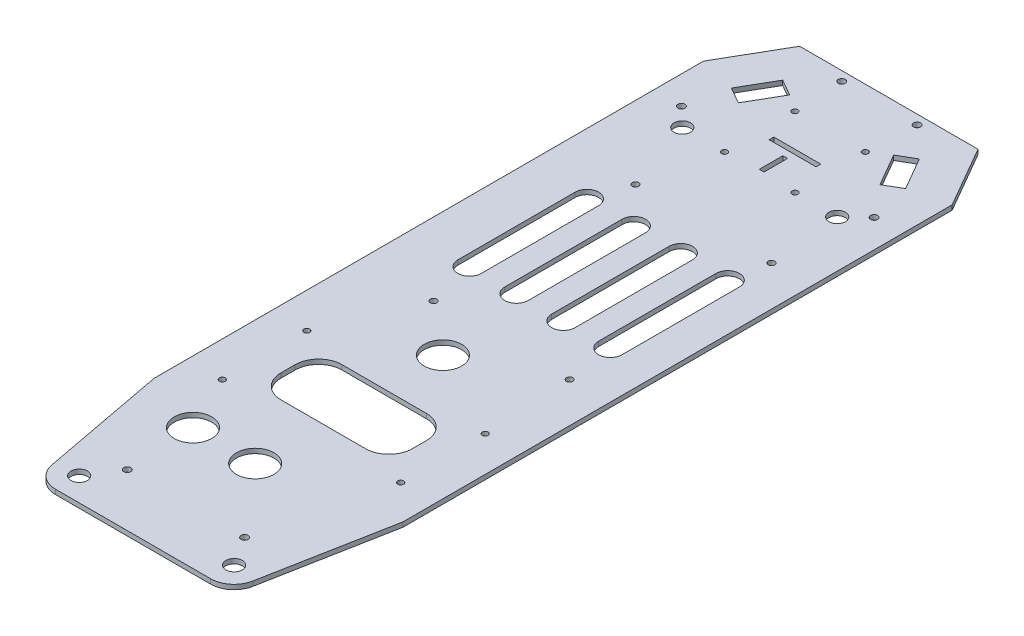
SolidWorks part; units mm, degrees
material "Epoxy, renforcé"
ref_plane "Plan de face" through (0, 0, 0) normal (0, 0, 1) x (1, 0, 0)
ref_plane "Plan de dessus" through (0, 0, 0) normal (0, 1, 0) x (1, 0, 0)
ref_plane "Plan de droite" through (0, 0, 0) normal (1, 0, 0) x (0, 0, -1)
sketch "Esquisse1" plane through (0, 0, 0) normal (0, 1, 0) x (1, 0, 0)
  line L0 (-33, 128.5) -> (33, 128.5) construction
  line L1 (33, 128.5) -> (33, -128.5) construction
  line L2 (33, -128.5) -> (-33, -128.5) construction
  line L3 (-33, -128.5) -> (-33, 128.5) construction
  line L4 (0, 128.5) -> (0, 0) construction
  line L5 (33, 0) -> (0, 0) construction
  line L6 (53, 183.5) -> (-53, 183.5)
  line L7 (-53, 183.5) -> (-53, -148.5)
  line L8 (-53, -148.5) -> (53, -148.5)
  line L9 (53, 183.5) -> (53, -148.5)
  circle A0 centre (-33, 128.5) radius 3.5
  circle A1 centre (-33, -128.5) radius 3.5
  circle A2 centre (33, 128.5) radius 3.5
  circle A3 centre (33, -128.5) radius 3.5
  point P17 (0, -148.5)
  point P18 (0, 183.5)
  dimension "D1" = 7
  dimension "D2" = 7
  dimension "D3" = 7
  dimension "D4" = 7
  dimension "D5" = 66
  dimension "D6" = 257
  dimension "D7" = 55
  dimension "D8" = 20
  dimension "D9" = 20
extrude "Boss.-Extru.1" add sketch "Esquisse1" along normal blind 2
sketch "Esquisse3" plane through (0, 2, 0) normal (0, 1, 0) x (1, 0, 0)
  line L0 (-22, 11.5) -> (-22, 97.5) construction
  line L1 (-22, 97.5) -> (36, 97.5) construction
  line L2 (36, 97.5) -> (36, 11.5) construction
  line L3 (36, 11.5) -> (-22, 11.5) construction
  line L4 (53, -148.5) -> (53, 183.5) construction
  line L5 (53, 183.5) -> (-53, 183.5) construction
  circle A4 centre (-22, 11.5) radius 1.375
  circle A5 centre (-22, 97.5) radius 1.375
  circle A6 centre (36, 97.5) radius 1.375
  circle A7 centre (36, 11.5) radius 1.375
  dimension "D1" = 86
  dimension "D2" = 58
  dimension "D3" = 17
  dimension "D4" = 86
extrude "Enlèv. mat.-Extru.1" cut sketch "Esquisse3" against normal through all
chamfer "Chanfrein1" distance 15 angle 60 2 edges at (-53, 1, -183.5) (53, 1, -183.5)
sketch "Esquisse4" plane through (0, 2, 0) normal (0, 1, 0) x (1, 0, 0)
  line L0 (0, -62.5) -> (0, -148.5) construction
  line L1 (38, -62.5) -> (-38, -62.5) construction
  line L2 (38, -62.5) -> (38, -26.5) construction
  line L3 (38, -26.5) -> (-38, -26.5) construction
  line L4 (-38, -62.5) -> (-38, -26.5) construction
  line L5 (-53, -148.5) -> (53, -148.5) construction
  line L6 (38, 183.5) -> (-38, 183.5) construction
  line L7 (-28, -57.5) -> (28, -57.5)
  line L8 (-28, -57.5) -> (-28, -31.5)
  line L9 (-28, -31.5) -> (28, -31.5)
  line L10 (28, -57.5) -> (28, -31.5)
  circle A0 centre (38, -62.5) radius 1.25
  circle A1 centre (38, -26.5) radius 1.25
  circle A2 centre (-38, -62.5) radius 1.25
  circle A3 centre (-38, -26.5) radius 1.25
  dimension "D3" = 2.5
  dimension "D4" = 2.5
  dimension "D5" = 2.5
  dimension "D6" = 2.5
  dimension "D1" = 76
  dimension "D2" = 36
  dimension "D7" = 210
  dimension "D8" = 10
  dimension "D9" = 10
  dimension "D10" = 10
  dimension "D11" = 10
extrude "Enlèv. mat.-Extru.2" cut sketch "Esquisse4" against normal blind 10
fillet "Congé1" radius 10 4 edges at (28, 1, 57.5) (28, 1, 31.5) (-28, 1, 31.5) (-28, 1, 57.5)
sketch "Esquisse5" plane through (0, 2, 0) normal (0, 1, 0) x (1, 0, 0)
  line L1 (-22, 11.5) -> (36, 11.5) construction
  line L2 (-22, 11.5) -> (-22, 97.5) construction
  line L3 (-22, 97.5) -> (36, 97.5) construction
  line L4 (36, 11.5) -> (36, 97.5) construction
  line L5 (-17, 16.5) -> (23.5, 16.5)
  line L6 (-17, 16.5) -> (-17, 92.5)
  line L7 (-17, 92.5) -> (23.5, 92.5)
  line L8 (23.5, 16.5) -> (23.5, 92.5)
  dimension "D1" = 10
  dimension "D2" = 10
  dimension "D3" = 25
  dimension "D4" = 10
extrude "Enlèv. mat.-Extru.3" [suppressed] cut sketch "Esquisse5" against normal blind 10
fillet "Congé2" [suppressed] radius 10
sketch "Esquisse6" plane through (0, 2, 0) normal (0, 1, 0) x (1, 0, 0)
  line L0 (0, 183.5) -> (0, 143.5) construction
  line L2 (38, 183.5) -> (-38, 183.5) construction
  line L3 (15, 128.5) -> (-15, 128.5) construction
  line L4 (15, 128.5) -> (15, 158.5) construction
  line L5 (15, 158.5) -> (-15, 158.5) construction
  line L6 (-15, 128.5) -> (-15, 158.5) construction
  line L7 (15, 128.5) -> (-15, 158.5) construction
  line L8 (15, 158.5) -> (-15, 128.5) construction
  line L9 (-10, 142.5) -> (10, 142.5)
  line L10 (-10, 142.5) -> (-10, 144.5)
  line L11 (-10, 144.5) -> (10, 144.5)
  line L12 (10, 142.5) -> (10, 144.5)
  line L13 (-10, 142.5) -> (10, 144.5) construction
  line L14 (-10, 144.5) -> (10, 142.5) construction
  line L15 (-1.1799, 129.5) -> (0.8201, 129.5)
  line L16 (-1.1799, 129.5) -> (-1.1799, 139.5)
  line L17 (-1.1799, 139.5) -> (0.8201, 139.5)
  line L18 (0.8201, 129.5) -> (0.8201, 139.5)
  line L19 (-1.1799, 129.5) -> (0.8201, 139.5) construction
  line L20 (-1.1799, 139.5) -> (0.8201, 129.5) construction
  circle A0 centre (-15, 128.5) radius 1.25
  circle A1 centre (15, 128.5) radius 1.25
  circle A2 centre (-15, 158.5) radius 1.25
  circle A3 centre (15, 158.5) radius 1.25
  point P16 (-0.1799, 134.5)
  dimension "D4" = 2.5
  dimension "D5" = 2.5
  dimension "D6" = 2.5
  dimension "D7" = 2.5
  dimension "D1" = 30
  dimension "D2" = 30
  dimension "D3" = 40
  dimension "D8" = 20
  dimension "D9" = 2
  dimension "D10" = 10
  dimension "D11" = 2
  dimension "D12" = 3
extrude "Enlèv. mat.-Extru.4" cut sketch "Esquisse6" against normal blind 10
sketch "Esquisse7" plane through (0, 2, 0) normal (0, 1, 0) x (1, 0, 0)
  line L0 (0, -86.5) -> (0, -148.5) construction
  line L1 (-53, -148.5) -> (53, -148.5) construction
  line L2 (0, -86.5) -> (-53, -86.5) construction
  line L3 (-53, 157.5192) -> (-53, -148.5) construction
  line L4 (38, 183.5) -> (-38, 183.5) construction
  circle A0 centre (0, -86.5) radius 8
  circle A1 centre (-26.5, -86.5) radius 8
  dimension "D1" = 16
  dimension "D3" = 16
  dimension "D2" = 270
extrude "Enlèv. mat.-Extru.5" cut sketch "Esquisse7" against normal blind 10
sketch "Esquisse8" plane through (0, 2, 0) normal (0, 1, 0) x (1, 0, 0)
  line L0 (38, 183.5) -> (-38, 183.5)
  line L1 (38, 183.5) -> (-38, 183.5) construction
  line L2 (-38, 183.5) -> (-53, 157.5192)
  line L3 (-53, 157.5192) -> (-53, -76.5)
  line L4 (-53, 157.5192) -> (-53, -148.5) construction
  line L5 (-53, -76.5) -> (-42.8262, -130.3562)
  line L6 (-33, -138.5) -> (33, -138.5)
  line L7 (0, -148.5) -> (0, 183.5) construction
  line L8 (-53, -148.5) -> (53, -148.5) construction
  line L9 (53, -76.5) -> (42.8262, -130.3562)
  line L10 (53, 157.5192) -> (53, -76.5)
  line L11 (38, 183.5) -> (53, 157.5192)
  arc A0 (-42.8262, -130.3562) -> (-33, -138.5) centre (-33, -128.5) ccw
  arc A1 (42.8262, -130.3562) -> (33, -138.5) centre (33, -128.5) cw
  point P22 (0, -138.5)
  dimension "D1" = 20
  dimension "D2" = 260
extrude "Enlèv. mat.-Extru.6" cut sketch "Esquisse8" against normal blind 10 flip side to cut
sketch "Esquisse9" plane through (0, 2, 0) normal (0, 1, 0) x (1, 0, 0)
  line L0 (53, 10.4239) -> (-53, 10.4239) construction
  line L1 (53, -76.5) -> (53, 157.5192) construction
  line L2 (-53, 157.5192) -> (-53, -76.5) construction
  circle A0 centre (45, 10.4239) radius 3.5
  circle A1 centre (-45, 10.4239) radius 3.5
  dimension "D1" = 7
  dimension "D3" = 7
  dimension "D2" = 8
  dimension "D4" = 8
extrude "Enlèv. mat.-Extru.7" [suppressed] cut sketch "Esquisse9" against normal blind 10
sketch "Esquisse10" plane through (0, 0, 0) normal (0, -1, 0) x (1, 0, 0)
  line L0 (38, -183.5) -> (53, -157.5192) construction
  line L1 (55.5, -153.1891) -> (37.3135, -142.6891) construction
  line L2 (55.5, -153.1891) -> (38, -183.5) construction
  line L3 (38, -183.5) -> (19.8135, -173) construction
  line L4 (37.3135, -142.6891) -> (19.8135, -173) construction
  line L5 (55.5, -153.1891) -> (19.8135, -173) construction
  line L6 (38, -183.5) -> (37.3135, -142.6891) construction
  line L7 (28.5635, -157.8446) -> (37.6567, -163.0946) construction
  line L8 (32.5635, -150.9164) -> (30.1819, -149.5414)
  line L9 (30.1819, -149.5414) -> (26.1868, -156.461)
  line L10 (32.5635, -150.9164) -> (37.1101, -153.5414)
  line L11 (37.1101, -153.5414) -> (29.1101, -167.3978)
  line L12 (24.5635, -164.7728) -> (29.1101, -167.3978)
  line L13 (22.1819, -163.3978) -> (26.1868, -156.461)
  line L14 (24.5635, -164.7728) -> (22.1819, -163.3978)
  line L15 (0, -183.5) -> (0, -146.2698) construction
  line L16 (28.5635, -157.8446) -> (16.0635, -179.4952) construction
  line L18 (38, -183.5) -> (-38, -183.5) construction
  line L19 (-28.5635, -157.8446) -> (-37.6567, -163.0946) construction
  line L20 (-38, -183.5) -> (-37.3135, -142.6891) construction
  line L21 (-55.5, -153.1891) -> (-19.8135, -173) construction
  line L22 (-37.3135, -142.6891) -> (-19.8135, -173) construction
  line L23 (-38, -183.5) -> (-19.8135, -173) construction
  line L24 (-55.5, -153.1891) -> (-38, -183.5) construction
  line L25 (-55.5, -153.1891) -> (-37.3135, -142.6891) construction
  line L26 (-24.5635, -164.7728) -> (-22.1819, -163.3978)
  line L27 (-22.1819, -163.3978) -> (-26.1868, -156.461)
  line L28 (-24.5635, -164.7728) -> (-29.1101, -167.3978)
  line L29 (-37.1101, -153.5414) -> (-29.1101, -167.3978)
  line L30 (-32.5635, -150.9164) -> (-37.1101, -153.5414)
  line L31 (-30.1819, -149.5414) -> (-26.1868, -156.461)
  line L32 (-32.5635, -150.9164) -> (-30.1819, -149.5414)
  circle A0 centre (16.0635, -179.4952) radius 1.5
  circle A1 centre (41.0635, -136.1939) radius 1.5
  circle A2 centre (-41.0635, -136.1939) radius 1.5
  circle A3 centre (-16.0635, -179.4952) radius 1.5
  point P0 (37.6567, -163.0946)
  point P16 (33.1101, -160.4696)
  point P38 (-33.1101, -160.4696)
  dimension "D3" = 8
  dimension "D5" = 3
  dimension "D1" = 21
  dimension "D2" = 35
  dimension "D4" = 8
  dimension "D6" = 25
extrude "Enlèv. mat.-Extru.8" cut sketch "Esquisse10" against normal blind 10
sketch "Esquisse11" plane through (0, 0, 0) normal (0, -1, 0) x (1, 0, 0)
  line L0 (25, 116) -> (0, 116) construction
  line L1 (17.5, 126.5) -> (-17.5, 126.5) construction
  line L2 (17.5, 126.5) -> (17.5, 105.5) construction
  line L3 (17.5, 105.5) -> (-17.5, 105.5) construction
  line L4 (-17.5, 126.5) -> (-17.5, 105.5) construction
  line L5 (17.5, 126.5) -> (-17.5, 105.5) construction
  line L6 (17.5, 105.5) -> (-17.5, 126.5) construction
  line L7 (0, 116) -> (0, 105.5) construction
  line L8 (0, 138.5) -> (0, 126.5) construction
  line L9 (-33, 138.5) -> (33, 138.5) construction
  circle A0 centre (25, 116) radius 1.5
  circle A1 centre (-25, 116) radius 1.5
  point P0 (0, 116)
  dimension "D3" = 3
  dimension "D1" = 21
  dimension "D2" = 35
  dimension "D4" = 25
  dimension "D5" = 12
extrude "Enlèv. mat.-Extru.9" cut sketch "Esquisse11" against normal blind 10
sketch "Esquisse12" plane through (0, 0, 0) normal (0, -1, 0) x (1, 0, 0)
  line L0 (33, -31.8433) -> (33, -81.8433) construction
  line L1 (38, -31.8433) -> (38, -81.8433)
  line L2 (28, -31.8433) -> (28, -81.8433)
  line L3 (13, -31.8433) -> (13, -81.8433) construction
  line L4 (18, -31.8433) -> (18, -81.8433)
  line L5 (8, -31.8433) -> (8, -81.8433)
  line L6 (-7, -31.8433) -> (-7, -81.8433) construction
  line L7 (-2, -31.8433) -> (-2, -81.8433)
  line L8 (-12, -31.8433) -> (-12, -81.8433)
  line L9 (-27, -31.8433) -> (-27, -81.8433) construction
  line L10 (-22, -31.8433) -> (-22, -81.8433)
  line L11 (-32, -31.8433) -> (-32, -81.8433)
  line L12 (53, 76.5) -> (53, -157.5192) construction
  arc A0 (38, -31.8433) -> (28, -31.8433) centre (33, -31.8433) ccw
  arc A1 (28, -81.8433) -> (38, -81.8433) centre (33, -81.8433) ccw
  arc A2 (18, -31.8433) -> (8, -31.8433) centre (13, -31.8433) ccw
  arc A3 (8, -81.8433) -> (18, -81.8433) centre (13, -81.8433) ccw
  arc A4 (-2, -31.8433) -> (-12, -31.8433) centre (-7, -31.8433) ccw
  arc A5 (-12, -81.8433) -> (-2, -81.8433) centre (-7, -81.8433) ccw
  arc A6 (-22, -31.8433) -> (-32, -31.8433) centre (-27, -31.8433) ccw
  arc A7 (-32, -81.8433) -> (-22, -81.8433) centre (-27, -81.8433) ccw
  point P2 (33, -56.8433)
  point P10 (13, -56.8433)
  point P17 (-7, -56.8433)
  point P24 (-27, -56.8433)
  dimension "D1" = 10
  dimension "D2" = 50
  dimension "D4" = 20
  dimension "D3" = 4
extrude "Enlèv. mat.-Extru.10" cut sketch "Esquisse12" against normal blind 10
sketch "Esquisse13" plane through (0, 0, 0) normal (0, -1, 0) x (1, 0, 0)
  line L0 (0, 138.5) -> (0, 0) construction
  line L1 (-33, 138.5) -> (33, 138.5) construction
  line L2 (18, 31.5) -> (-18, 31.5) construction
  circle A0 centre (0, 6.5) radius 8
  dimension "D1" = 16
  dimension "D2" = 25
extrude "Enlèv. mat.-Extru.11" cut sketch "Esquisse13" against normal blind 10
